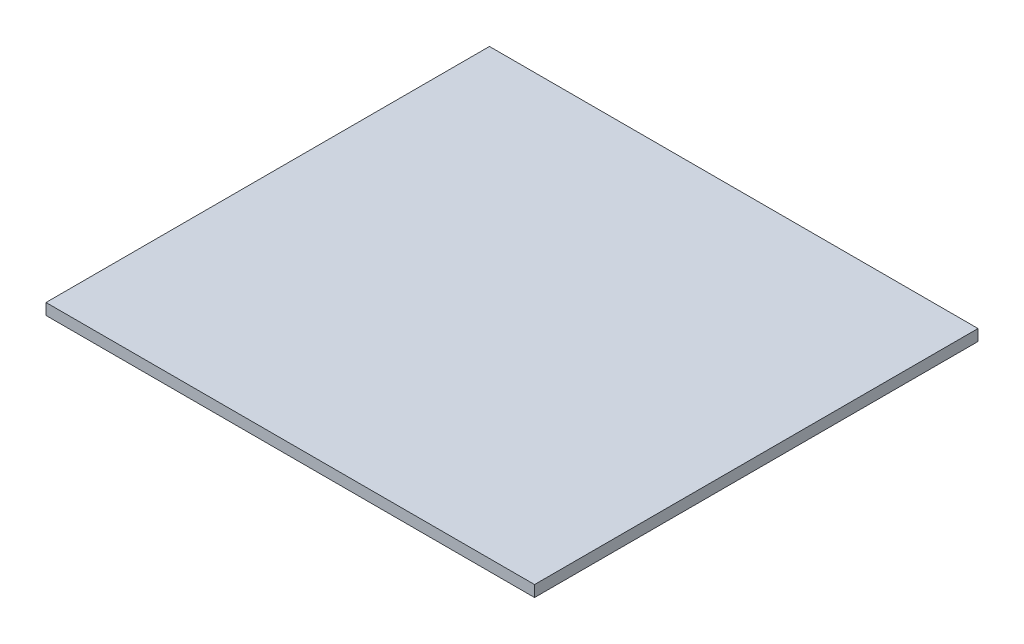
SolidWorks part; units mm, degrees
ref_plane "Front Plane" through (0, 0, 0) normal (0, 0, 1) x (1, 0, 0)
ref_plane "Top Plane" through (0, 0, 0) normal (0, 1, 0) x (1, 0, 0)
ref_plane "Right Plane" through (0, 0, 0) normal (1, 0, 0) x (0, 0, -1)
sketch "Sketch1" plane through (0, 0, 0) normal (0, 1, 0) x (1, 0, 0)
  line L1 (-106.1328, 64.8539) -> (23.8672, 64.8539)
  line L2 (-106.1328, 64.8539) -> (-106.1328, -53.1461)
  line L3 (-106.1328, -53.1461) -> (23.8672, -53.1461)
  line L4 (23.8672, 64.8539) -> (23.8672, -53.1461)
  dimension "D1" = 118
  dimension "D2" = 130
extrude "Boss-Extrude2" add sketch "Sketch1" along normal blind 3
